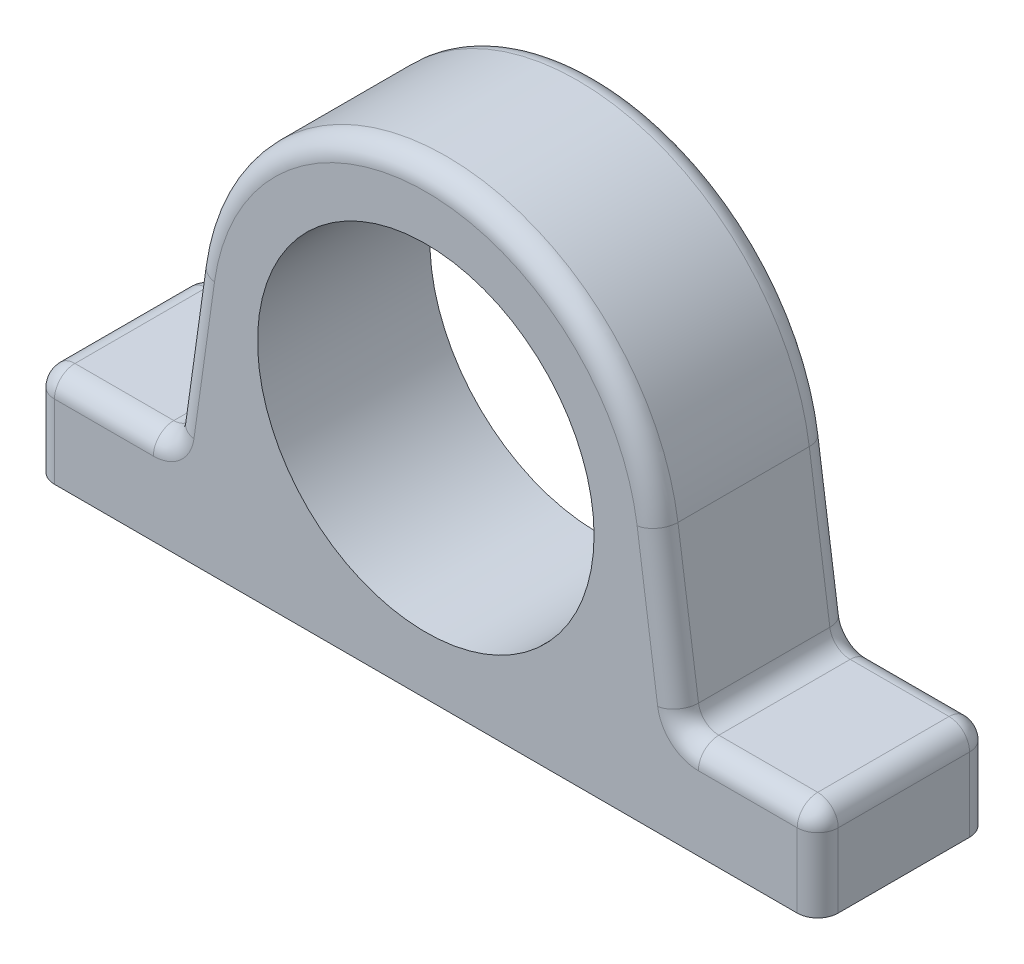
SolidWorks part; units mm, degrees
ref_plane "Front Plane" through (0, 0, 0) normal (0, 0, 1) x (1, 0, 0)
ref_plane "Top Plane" through (0, 0, 0) normal (0, 1, 0) x (1, 0, 0)
ref_plane "Right Plane" through (0, 0, 0) normal (1, 0, 0) x (0, 0, -1)
sketch "Sketch1" plane through (0, 0, 0) normal (0, 0, 1) x (1, 0, 0)
  line L0 (0, 0) -> (-95.5, 0)
  line L1 (-95.5, 0) -> (-95.5, 23)
  line L2 (-56.4453, 62.9329) -> (-62.0575, 23)
  line L3 (-62.0575, 23) -> (-95.5, 23)
  line L4 (0, 112) -> (0, 96)
  line L5 (0, 14) -> (0, 0)
  arc A0 (0, 96) -> (0, 14) centre (0, 55) ccw
  arc A1 (-56.4453, 62.9329) -> (0, 112) centre (0, 55) cw
  dimension "D6" = 41
  dimension "D1" = 95.5
  dimension "D2" = 55
  dimension "D3" = 23
  dimension "D4" = 112
  dimension "D5" = 8
extrude "Boss-Extrude1" add sketch "Sketch1" along normal blind 42
mirror "Mirror1" about plane through (0, 112, 42) normal (-1, 0, 0) of "Boss-Extrude1"
fillet "Fillet1" radius 5 18 edges at (59.2514, 42.9664, 0) (59.2514, 42.9664, 42) (0, 112, 42) (-78.7787, 23, 42) (-95.5, 23, 21) (-78.7787, 23, 0) (-59.2514, 42.9664, 42) (-62.0575, 23, 21) (-59.2514, 42.9664, 0) (95.5, 11.5, 0) (95.5, 11.5, 42) (95.5, 23, 21) (-95.5, 11.5, 0) (-95.5, 11.5, 42) (62.0575, 23, 21) (78.7787, 23, 0) (78.7787, 23, 42) (0, 112, 0)
